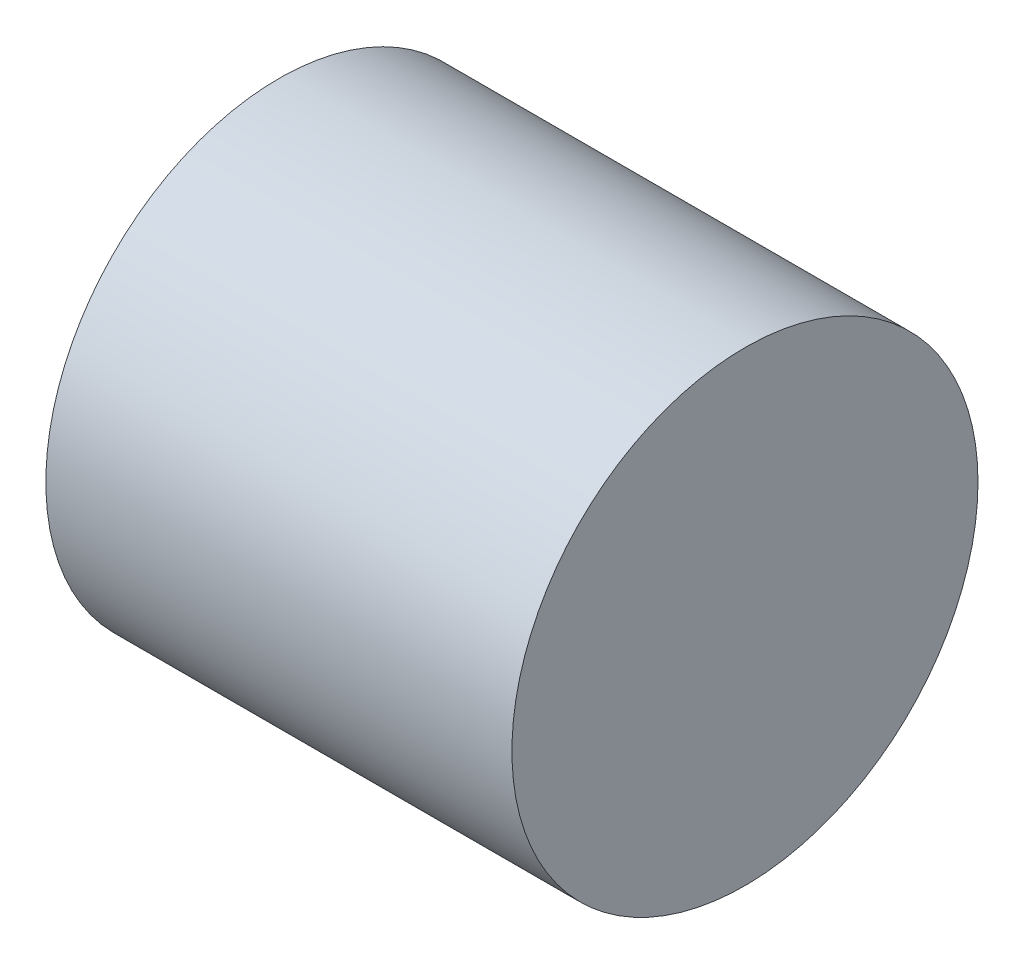
SolidWorks part; units mm, degrees
ref_plane "Front Plane" through (0, 0, 0) normal (0, 0, 1) x (1, 0, 0)
ref_plane "Top Plane" through (0, 0, 0) normal (0, 1, 0) x (1, 0, 0)
ref_plane "Right Plane" through (0, 0, 0) normal (1, 0, 0) x (0, 0, -1)
sketch "Sketch1" plane through (0, 0, 0) normal (1, 0, 0) x (0, 0, -1)
  circle A0 centre (0, 0) radius 20
extrude "Boss-Extrude1" add sketch "Sketch1" along normal blind 40
